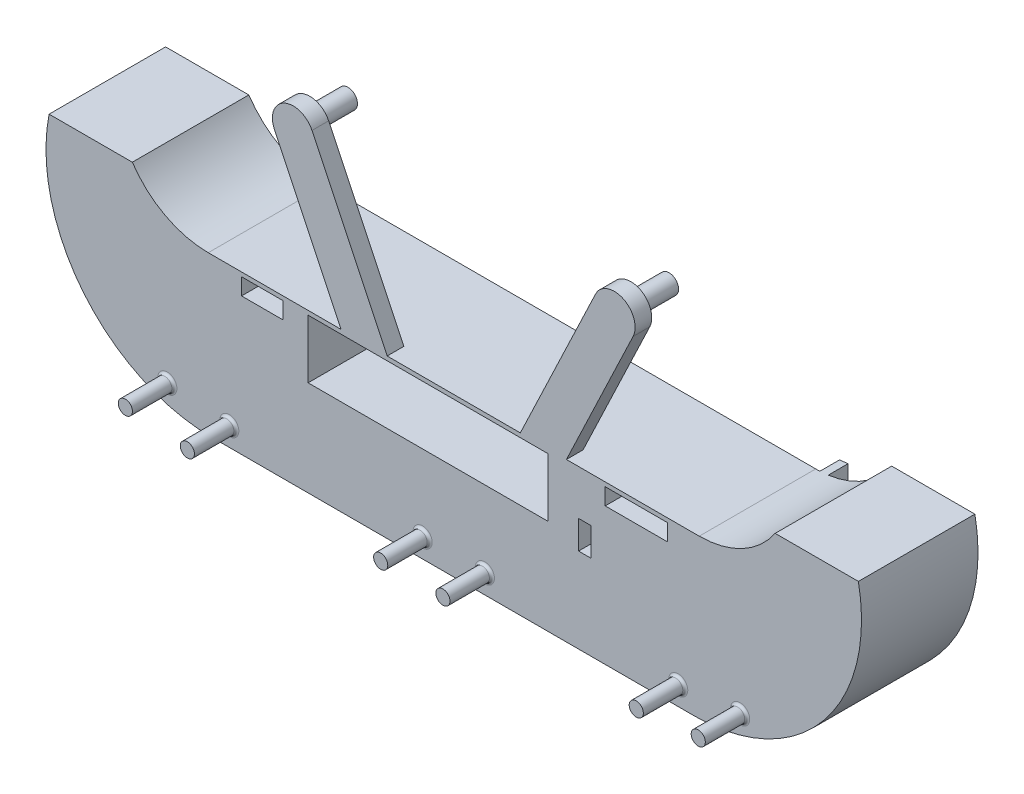
SolidWorks part; units mm, degrees
ref_plane "Front Plane" through (0, 0, 0) normal (0, 0, 1) x (1, 0, 0)
ref_plane "Top Plane" through (0, 0, 0) normal (0, 1, 0) x (1, 0, 0)
ref_plane "Right Plane" through (0, 0, 0) normal (1, 0, 0) x (0, 0, -1)
sketch "Sketch1" plane through (0, 0, 0) normal (0, 0, 1) x (1, 0, 0)
  line L0 (47.8782, -181.4728) -> (47.8782, -219.1826) construction
  line L1 (26.2444, -195.1068) -> (37.7182, -219.1826)
  line L2 (20.512, -197.8387) -> (30.684, -219.1826)
  line L3 (37.7182, -219.1826) -> (58.0382, -219.1826)
  line L5 (30.684, -219.1826) -> (10.4132, -219.1826)
  line L6 (10.4132, -219.1826) -> (10.4132, -233.1526)
  line L7 (10.4132, -233.1526) -> (85.3432, -233.1526)
  line L8 (85.3432, -219.1826) -> (85.3432, -233.1526)
  line L9 (65.0724, -219.1826) -> (85.3432, -219.1826)
  line L10 (75.2444, -197.8387) -> (65.0724, -219.1826)
  line L11 (69.512, -195.1068) -> (58.0382, -219.1826)
  line L12 (47.8782, -233.1526) -> (47.8782, -250.7641) construction
  arc A0 (26.2444, -195.1068) -> (20.512, -197.8387) centre (23.3782, -196.4728) ccw
  arc A1 (69.512, -195.1068) -> (75.2444, -197.8387) centre (72.3782, -196.4728) cw
  dimension "D1" = 6.35
  dimension "D3" = 10.16
  dimension "D2" = 26.67
  dimension "D4" = 13.97
  dimension "D5" = 74.93
extrude "Boss-Extrude1" add sketch "Sketch1" along normal blind 6.35
sketch "Sketch2" plane through (0, 0, 0) normal (0, 0, -1) x (-1, 0, 0)
  circle A1 centre (-23.3782, -196.4728) radius 1.4605
  circle A3 centre (-72.3782, -196.4728) radius 1.4605
  dimension "D1" = 2.921
  dimension "D2" = 2.921
extrude "Boss-Extrude2" add sketch "Sketch2" along normal up to surface (2 mm away)
sketch "Sketch3" plane through (0, 0, 0) normal (0, 0, -1) x (-1, 0, 0)
  line L0 (-30.2252, -224.8976) -> (-30.2252, -219.8176)
  line L1 (-30.2252, -219.8176) -> (-59.6892, -219.8176)
  line L2 (-59.6892, -219.8176) -> (-59.6892, -224.8976)
  line L3 (-59.6892, -224.8976) -> (-30.2252, -224.8976)
  line L4 (-30.684, -219.1826) -> (-10.4132, -219.1826) construction
  line L5 (-10.4132, -219.1826) -> (-10.4132, -233.1526) construction
  line L6 (-15.4932, -219.8176) -> (-21.8432, -219.8176)
  line L7 (-21.8432, -219.8176) -> (-21.8432, -222.3576)
  line L8 (-21.8432, -222.3576) -> (-15.4932, -222.3576)
  line L9 (-15.4932, -222.3576) -> (-15.4932, -219.8176)
  line L10 (-70.9922, -219.8176) -> (-70.9922, -222.3576)
  line L11 (-70.9922, -222.3576) -> (-80.5172, -222.3576)
  line L12 (-80.5172, -222.3576) -> (-80.5172, -219.8176)
  line L13 (-80.5172, -219.8176) -> (-70.9922, -219.8176)
  line L14 (-85.3432, -219.1826) -> (-65.0724, -219.1826) construction
  line L15 (-66.9282, -230.3586) -> (-66.9282, -226.0406)
  line L16 (-66.9282, -226.0406) -> (-68.8332, -226.0406)
  line L17 (-68.8332, -226.0406) -> (-68.8332, -230.3586)
  line L18 (-68.8332, -230.3586) -> (-66.9282, -230.3586)
  line L19 (-10.4132, -233.1526) -> (-85.3432, -233.1526) construction
  line L20 (-85.3432, -233.1526) -> (-85.3432, -219.1826) construction
  dimension "D1" = 5.08
  dimension "D2" = 0.635
  dimension "D3" = 29.464
  dimension "D4" = 19.812
  dimension "D5" = 6.35
  dimension "D6" = 2.54
  dimension "D7" = 5.08
  dimension "D8" = 9.525
  dimension "D9" = 2.54
  dimension "D10" = 4.826
  dimension "D11" = 0.635
  dimension "D12" = 1.905
  dimension "D13" = 4.318
  dimension "D14" = 2.794
  dimension "D15" = 16.51
extrude "Cut-Extrude1" cut sketch "Sketch3" against normal blind 3.81
sketch "Sketch4" plane through (0, 0, 0) normal (0, 0, -1) x (-1, 0, 0)
  arc A0 (-11.861, -222.3576) -> (-14.0454, -222.3576) centre (-12.9532, -222.3576) ccw construction
  arc A1 (-14.0454, -222.3576) -> (-11.861, -222.3576) centre (-12.9532, -222.3576) ccw construction
  arc A2 (-11.861, -222.3576) -> (-14.0454, -222.3576) centre (-12.9532, -222.3576) ccw
  arc A3 (-14.0454, -222.3576) -> (-11.861, -222.3576) centre (-12.9532, -222.3576) ccw
  arc A4 (-62.661, -222.3576) -> (-64.8454, -222.3576) centre (-63.7532, -222.3576) ccw construction
  arc A5 (-64.8454, -222.3576) -> (-62.661, -222.3576) centre (-63.7532, -222.3576) ccw construction
  arc A6 (-67.741, -222.3576) -> (-69.9254, -222.3576) centre (-68.8332, -222.3576) ccw construction
  arc A7 (-69.9254, -222.3576) -> (-67.741, -222.3576) centre (-68.8332, -222.3576) ccw construction
  arc A8 (-81.711, -222.3576) -> (-83.8954, -222.3576) centre (-82.8032, -222.3576) ccw construction
  arc A9 (-83.8954, -222.3576) -> (-81.711, -222.3576) centre (-82.8032, -222.3576) ccw construction
  arc A10 (-62.661, -222.3576) -> (-64.8454, -222.3576) centre (-63.7532, -222.3576) ccw
  arc A11 (-64.8454, -222.3576) -> (-62.661, -222.3576) centre (-63.7532, -222.3576) ccw
  arc A12 (-67.741, -222.3576) -> (-69.9254, -222.3576) centre (-68.8332, -222.3576) ccw
  arc A13 (-69.9254, -222.3576) -> (-67.741, -222.3576) centre (-68.8332, -222.3576) ccw
  arc A14 (-81.711, -222.3576) -> (-83.8954, -222.3576) centre (-82.8032, -222.3576) ccw
  arc A15 (-83.8954, -222.3576) -> (-81.711, -222.3576) centre (-82.8032, -222.3576) ccw
extrude "Boss-Extrude3" add sketch "Sketch4" along normal up to surface (1.5748 mm away)
sketch "Sketch5" plane through (0, 0, 0) normal (0, 0, -1) x (-1, 0, 0)
  line L1 (13.8751, -213.0146) -> (1.1751, -213.0146)
  line L2 (-47.8782, -243.3126) -> (-47.8782, -261.0941) construction
  line L3 (-85.3432, -233.1526) -> (-85.3432, -219.1826)
  line L5 (-30.684, -219.1826) -> (-10.4132, -219.1826) construction
  line L6 (-47.8782, -232.5176) -> (-47.8782, -247.3882) construction
  line L7 (-84.7082, -243.3126) -> (-11.0482, -243.3126)
  line L8 (-85.3432, -233.1526) -> (-10.4132, -233.1526)
  line L9 (-10.4132, -233.1526) -> (-10.4132, -219.1826)
  line L10 (-109.6315, -213.0146) -> (-96.9315, -213.0146)
  arc A0 (-10.4132, -219.1826) -> (1.1751, -213.0146) centre (-10.4132, -205.2126) ccw
  arc A2 (-11.0482, -243.3126) -> (13.8751, -213.0146) centre (-11.0482, -217.9126) ccw
  arc A3 (-85.3432, -219.1826) -> (-96.9315, -213.0146) centre (-85.3432, -205.2126) cw
  arc A4 (-84.7082, -243.3126) -> (-109.6315, -213.0146) centre (-84.7082, -217.9126) cw
  dimension "D1" = 12.7
  dimension "D4" = 25.4
  dimension "D5" = 10.16
  dimension "D2" = 13.97
  dimension "D3" = 36.83
extrude "Boss-Extrude4" add sketch "Sketch5" against normal blind 2.54
sketch "Sketch6" plane through (0, 0, 2.54) normal (0, 0, 1) x (1, 0, 0)
  line L0 (47.8782, -232.5176) -> (47.8782, -247.3882) construction
  line L1 (10.4132, -233.1526) -> (85.3432, -233.1526) construction
  line L2 (47.8782, -243.4865) -> (47.8782, -250.2335) construction
  circle A0 centre (52.6282, -240.3916) radius 1.0795
  circle A1 centre (43.1282, -240.3916) radius 1.0795
  circle A2 centre (4.1664, -239.5331) radius 1.0795
  circle A3 centre (13.6235, -240.4343) radius 1.0795
  circle A4 centre (82.1329, -240.4343) radius 1.0795
  circle A5 centre (91.59, -239.5331) radius 1.0795
  dimension "D1" = 2.159
  dimension "D2" = 2.159
  dimension "D7" = 2.159
  dimension "D8" = 2.159
  dimension "D3" = 9.5
  dimension "D4" = 4.75
  dimension "D5" = 7.239
  dimension "D6" = 9.5
extrude "Boss-Extrude5" add sketch "Sketch6" along normal blind 6.4
sketch "Sketch7" plane through (0, 0, 0) normal (0, 0, -1) x (-1, 0, 0)
  line L0 (-30.684, -219.1826) -> (-37.7182, -219.1826)
  line L1 (-58.0382, -219.1826) -> (-65.0724, -219.1826)
  line L2 (-30.2252, -219.8176) -> (-59.6892, -219.8176) construction
  line L3 (-59.6892, -219.8176) -> (-59.6892, -224.8976) construction
  line L4 (-59.6892, -224.8976) -> (-30.2252, -224.8976) construction
  line L5 (-30.2252, -224.8976) -> (-30.2252, -219.8176) construction
  line L6 (-70.9922, -219.8176) -> (-80.5172, -219.8176) construction
  line L7 (-80.5172, -219.8176) -> (-80.5172, -222.3576) construction
  line L8 (-80.5172, -222.3576) -> (-70.9922, -222.3576) construction
  line L9 (-70.9922, -222.3576) -> (-70.9922, -219.8176) construction
  line L10 (-65.0724, -219.1826) -> (-85.3432, -219.1826)
  line L11 (-96.9315, -213.0146) -> (-109.6315, -213.0146)
  line L12 (-84.7082, -243.3126) -> (-11.0482, -243.3126)
  line L13 (13.8751, -213.0146) -> (1.1751, -213.0146)
  line L14 (-10.4132, -219.1826) -> (-30.684, -219.1826)
  line L15 (-30.684, -219.1826) -> (-20.512, -197.8387)
  line L16 (-26.2444, -195.1068) -> (-37.7182, -219.1826)
  line L17 (-37.7182, -219.1826) -> (-58.0382, -219.1826)
  line L18 (-58.0382, -219.1826) -> (-69.512, -195.1068)
  line L19 (-75.2444, -197.8387) -> (-65.0724, -219.1826)
  line L20 (-65.0724, -219.1826) -> (-85.3432, -219.1826)
  line L21 (-96.9315, -213.0146) -> (-109.6315, -213.0146)
  line L22 (-84.7082, -243.3126) -> (-11.0482, -243.3126)
  line L23 (13.8751, -213.0146) -> (1.1751, -213.0146)
  line L24 (-10.4132, -219.1826) -> (-30.684, -219.1826)
  line L27 (-37.7182, -219.1826) -> (-58.0382, -219.1826)
  line L30 (-68.8332, -230.3586) -> (-66.9282, -230.3586) construction
  line L31 (-66.9282, -230.3586) -> (-66.9282, -226.0406) construction
  line L32 (-66.9282, -226.0406) -> (-68.8332, -226.0406) construction
  line L33 (-68.8332, -226.0406) -> (-68.8332, -230.3586) construction
  line L34 (-15.4932, -222.3576) -> (-15.4932, -219.8176) construction
  line L35 (-15.4932, -219.8176) -> (-21.8432, -219.8176) construction
  line L36 (-21.8432, -219.8176) -> (-21.8432, -222.3576) construction
  line L37 (-21.8432, -222.3576) -> (-15.4932, -222.3576) construction
  line L38 (-30.2252, -219.8176) -> (-59.6892, -219.8176)
  line L39 (-59.6892, -219.8176) -> (-59.6892, -224.8976)
  line L40 (-59.6892, -224.8976) -> (-30.2252, -224.8976)
  line L41 (-30.2252, -224.8976) -> (-30.2252, -219.8176)
  line L42 (-70.9922, -219.8176) -> (-80.5172, -219.8176)
  line L43 (-80.5172, -219.8176) -> (-80.5172, -222.3576)
  line L44 (-80.5172, -222.3576) -> (-70.9922, -222.3576)
  line L45 (-70.9922, -222.3576) -> (-70.9922, -219.8176)
  line L46 (-68.8332, -230.3586) -> (-66.9282, -230.3586)
  line L47 (-66.9282, -230.3586) -> (-66.9282, -226.0406)
  line L48 (-66.9282, -226.0406) -> (-68.8332, -226.0406)
  line L49 (-68.8332, -226.0406) -> (-68.8332, -230.3586)
  line L50 (-15.4932, -222.3576) -> (-15.4932, -219.8176)
  line L51 (-15.4932, -219.8176) -> (-21.8432, -219.8176)
  line L52 (-21.8432, -219.8176) -> (-21.8432, -222.3576)
  line L53 (-21.8432, -222.3576) -> (-15.4932, -222.3576)
  circle A0 centre (-82.8032, -222.3576) radius 1.0922 construction
  circle A1 centre (-12.9532, -222.3576) radius 1.0922 construction
  circle A2 centre (-68.8332, -222.3576) radius 1.0922 construction
  circle A3 centre (-63.7532, -222.3576) radius 1.0922 construction
  circle A4 centre (-82.8032, -222.3576) radius 1.0922
  circle A5 centre (-12.9532, -222.3576) radius 1.0922
  arc A6 (-96.9315, -213.0146) -> (-85.3432, -219.1826) centre (-85.3432, -205.2126) ccw
  arc A7 (-109.6315, -213.0146) -> (-84.7082, -243.3126) centre (-84.7082, -217.9126) ccw
  arc A8 (-11.0482, -243.3126) -> (13.8751, -213.0146) centre (-11.0482, -217.9126) ccw
  arc A9 (-10.4132, -219.1826) -> (1.1751, -213.0146) centre (-10.4132, -205.2126) ccw
  arc A10 (-20.512, -197.8387) -> (-26.2444, -195.1068) centre (-23.3782, -196.4728) ccw
  arc A11 (-69.512, -195.1068) -> (-75.2444, -197.8387) centre (-72.3782, -196.4728) ccw
  arc A12 (-96.9315, -213.0146) -> (-85.3432, -219.1826) centre (-85.3432, -205.2126) ccw
  arc A13 (-109.6315, -213.0146) -> (-84.7082, -243.3126) centre (-84.7082, -217.9126) ccw
  arc A14 (-11.0482, -243.3126) -> (13.8751, -213.0146) centre (-11.0482, -217.9126) ccw
  arc A15 (-10.4132, -219.1826) -> (1.1751, -213.0146) centre (-10.4132, -205.2126) ccw
  circle A18 centre (-68.8332, -222.3576) radius 1.0922
  circle A19 centre (-63.7532, -222.3576) radius 1.0922
  dimension "D1" = 0
extrude "Boss-Extrude6" add sketch "Sketch7" along normal blind 15.24
sketch "Sketch8" plane through (0, 0, -2) normal (0, 0, -1) x (-1, 0, 0)
  circle A0 centre (-72.3782, -196.4728) radius 1.4605 construction
  circle A1 centre (-23.3782, -196.4728) radius 1.4605 construction
  circle A2 centre (-72.3782, -196.4728) radius 1.4605
  circle A3 centre (-23.3782, -196.4728) radius 1.4605
extrude "Boss-Extrude7" add sketch "Sketch8" along normal blind 3.81
sketch "Sketch9" plane through (0, 0, -15.24) normal (0, 0, -1) x (-1, 0, 0)
  circle A4 centre (-82.8032, -222.3576) radius 1.0668
  circle A5 centre (-63.7532, -222.3576) radius 1.0668
  circle A6 centre (-68.8332, -222.3576) radius 1.0668
  circle A7 centre (-12.9532, -222.3576) radius 1.0668
  dimension "D1" = 2.1336
  dimension "D2" = 2.1336
  dimension "D3" = 2.1336
  dimension "D4" = 2.1336
extrude "Boss-Extrude8" add sketch "Sketch9" along normal blind 1.778 and the other way up to surface
sketch "Sketch10" plane through (0, 0, -15.24) normal (0, 0, -1) x (-1, 0, 0)
  line L2 (-47.8782, -232.5176) -> (-47.8782, -247.3882) construction
  line L4 (-87.2482, -235.8161) -> (-8.5082, -235.8161)
  line L5 (-8.5082, -235.8161) -> (-8.5082, -219.0521)
  line L8 (-47.8782, -235.8161) -> (-47.8782, -253.4642) construction
  line L9 (-87.2482, -235.8161) -> (-87.2482, -219.0521)
  line L11 (-85.9782, -219.1681) -> (-85.9782, -233.2761)
  line L12 (-85.9782, -233.2761) -> (-9.7782, -233.2761)
  line L13 (-9.7782, -233.2761) -> (-9.7782, -219.1681)
  arc A0 (-10.4132, -219.1826) -> (1.1751, -213.0146) centre (-10.4132, -205.2126) ccw construction
  arc A3 (-9.7782, -219.1681) -> (-8.5082, -219.0521) centre (-10.4132, -205.2126) ccw
  arc A4 (-96.9315, -213.0146) -> (-85.3432, -219.1826) centre (-85.3432, -205.2126) ccw construction
  arc A5 (-87.2482, -219.0521) -> (-85.9782, -219.1681) centre (-85.3432, -205.2126) ccw
  dimension "D2" = 16.764
  dimension "D1" = 39.37
  dimension "D3" = 1.27
  dimension "D4" = 2.54
  dimension "D5" = 1.27
extrude "Boss-Extrude9" add sketch "Sketch10" along normal up to surface (3.0248 mm away)
fillet "Fillet1" radius 0.381 6 edges at (90.5105, -239.5331, 2.54) (81.0534, -240.4343, 2.54) (51.5487, -240.3916, 2.54) (42.0487, -240.3916, 2.54) (12.544, -240.4343, 2.54) (3.0869, -239.5331, 2.54)
sketch "Sketch12" plane through (0, 0, 6.35) normal (0, 0, 1) x (1, 0, 0)
  line L4 (59.6892, -219.8176) -> (30.2252, -219.8176)
  line L5 (59.6892, -224.8976) -> (59.6892, -219.8176)
  line L6 (30.2252, -224.8976) -> (59.6892, -224.8976)
  line L7 (30.2252, -219.8176) -> (30.2252, -224.8976)
  line L8 (59.6892, -219.8176) -> (30.2252, -219.8176)
  line L9 (59.6892, -224.8976) -> (59.6892, -219.8176)
  line L10 (30.2252, -224.8976) -> (59.6892, -224.8976)
  line L11 (30.2252, -219.8176) -> (30.2252, -224.8976)
  dimension "D1" = 0
extrude "Cut-Extrude2" cut sketch "Sketch12" against normal through all both and the other way through all
sketch "Sketch13" plane through (0, 0, 6.35) normal (0, 0, 1) x (1, 0, 0)
  line L1 (25.6532, -219.8176) -> (25.6532, -228.7584)
  line L2 (25.6532, -228.7584) -> (62.2292, -228.7584)
  line L3 (62.2292, -228.7584) -> (62.2292, -219.8176)
  line L5 (62.2292, -219.8176) -> (25.6532, -219.8176)
  line L6 (10.4132, -219.8176) -> (85.3432, -219.8176) construction
  line L7 (59.6892, -224.8976) -> (59.6892, -219.8176) construction
  dimension "D1" = 36.576
  dimension "D2" = 8.9408
  dimension "D3" = 8.9408
  dimension "D4" = 2.54
extrude "Cut-Extrude3" cut sketch "Sketch13" against normal through all both and the other way through all
sketch "Sketch14" plane through (0, 0, 6.35) normal (0, 0, 1) x (1, 0, 0)
  line L0 (62.2292, -219.8176) -> (25.6532, -219.8176) construction
  line L1 (25.6532, -219.8176) -> (25.6532, -228.7584) construction
  line L2 (62.2292, -228.7584) -> (62.2292, -219.8176) construction
  line L3 (25.6532, -228.7584) -> (62.2292, -228.7584) construction
  line L4 (62.2292, -219.8176) -> (25.6532, -219.8176)
  line L5 (25.6532, -219.8176) -> (25.6532, -228.7584)
  line L6 (62.2292, -228.7584) -> (62.2292, -219.8176)
  line L7 (25.6532, -228.7584) -> (62.2292, -228.7584)
  line L10 (85.3432, -219.1826) -> (65.0724, -219.1826)
  line L11 (65.0724, -219.1826) -> (75.2444, -197.8387)
  line L12 (69.512, -195.1068) -> (58.0382, -219.1826)
  line L13 (58.0382, -219.1826) -> (37.7182, -219.1826)
  line L14 (37.7182, -219.1826) -> (26.2444, -195.1068)
  line L15 (20.512, -197.8387) -> (30.684, -219.1826)
  line L16 (30.684, -219.1826) -> (10.4132, -219.1826)
  line L17 (10.4132, -219.1826) -> (10.4132, -233.1526)
  line L18 (10.4132, -233.1526) -> (85.3432, -233.1526)
  line L19 (85.3432, -233.1526) -> (85.3432, -219.1826)
  line L20 (85.3432, -219.1826) -> (65.0724, -219.1826)
  line L21 (65.0724, -219.1826) -> (75.2444, -197.8387)
  line L22 (69.512, -195.1068) -> (58.0382, -219.1826)
  line L23 (58.0382, -219.1826) -> (37.7182, -219.1826)
  line L24 (37.7182, -219.1826) -> (26.2444, -195.1068)
  line L25 (20.512, -197.8387) -> (30.684, -219.1826)
  line L26 (30.684, -219.1826) -> (10.4132, -219.1826)
  line L27 (10.4132, -219.1826) -> (10.4132, -233.1526)
  line L28 (10.4132, -233.1526) -> (85.3432, -233.1526)
  line L29 (85.3432, -233.1526) -> (85.3432, -219.1826)
  arc A2 (75.2444, -197.8387) -> (69.512, -195.1068) centre (72.3782, -196.4728) ccw
  arc A3 (26.2444, -195.1068) -> (20.512, -197.8387) centre (23.3782, -196.4728) ccw
  arc A4 (75.2444, -197.8387) -> (69.512, -195.1068) centre (72.3782, -196.4728) ccw
  arc A5 (26.2444, -195.1068) -> (20.512, -197.8387) centre (23.3782, -196.4728) ccw
  dimension "D1" = 0
extrude "Cut-Extrude4" cut sketch "Sketch14" against normal up to surface (3.81 mm away) and the other way through all up to face at (90.1295, -239.5331, 2.54)
